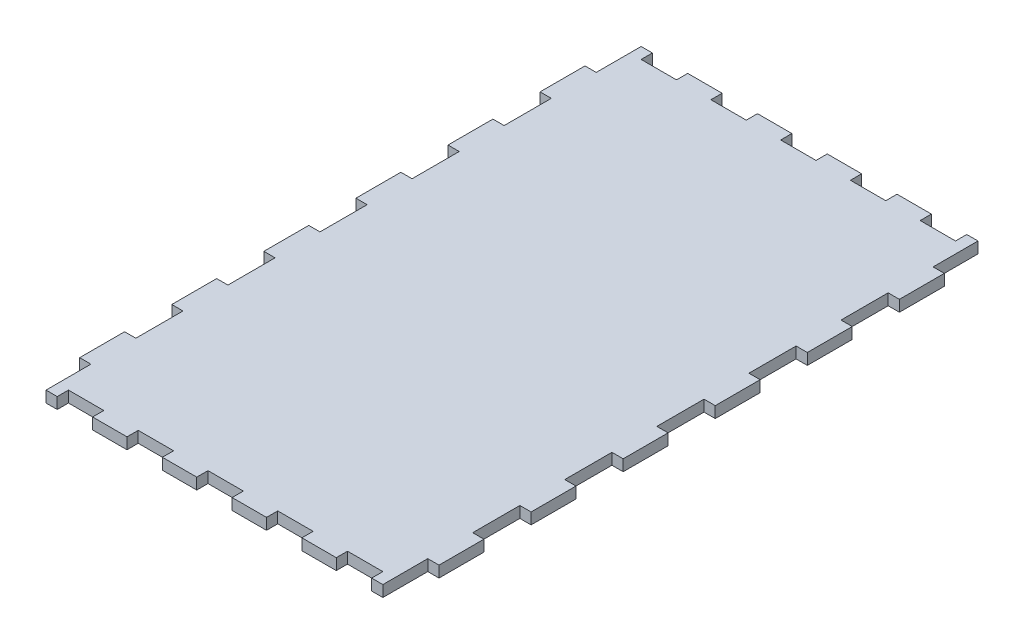
SolidWorks part; units mm, degrees
ref_plane "Front Plane" through (0, 0, 0) normal (0, 0, 1) x (1, 0, 0)
ref_plane "Top Plane" through (0, 0, 0) normal (0, 1, 0) x (1, 0, 0)
ref_plane "Right Plane" through (0, 0, 0) normal (1, 0, 0) x (0, 0, -1)
sketch "Sketch1" plane through (0, 0, 0) normal (0, 1, 0) x (1, 0, 0)
  line L0 (-80, 51.5) -> (-80, 30.5)
  line L1 (-80, 132.5) -> (80, 132.5)
  line L2 (-80, 132.5) -> (-80, -132.5)
  line L3 (-80, -132.5) -> (80, -132.5)
  line L4 (80, 132.5) -> (80, -132.5)
  line L5 (-80, 132.5) -> (80, -132.5) construction
  line L6 (-80, -132.5) -> (80, 132.5) construction
  line L7 (-80, 92.5) -> (-75, 92.5)
  line L8 (-80, 92.5) -> (-80, 71.5)
  line L9 (-80, 71.5) -> (-75, 71.5)
  line L10 (-75, 92.5) -> (-75, 71.5)
  line L11 (-80, 51.5) -> (-75, 51.5)
  line L12 (-75, 51.5) -> (-75, 30.5)
  line L13 (-80, 30.5) -> (-75, 30.5)
  line L14 (-80, 10.5) -> (-80, -10.5)
  line L15 (-80, 10.5) -> (-75, 10.5)
  line L16 (-75, 10.5) -> (-75, -10.5)
  line L17 (-80, -10.5) -> (-75, -10.5)
  line L18 (-80, -30.5) -> (-80, -51.5)
  line L19 (-80, -30.5) -> (-75, -30.5)
  line L20 (-75, -30.5) -> (-75, -51.5)
  line L21 (-80, -51.5) -> (-75, -51.5)
  line L22 (-80, -71.5) -> (-80, -92.5)
  line L23 (-80, -71.5) -> (-75, -71.5)
  line L24 (-75, -71.5) -> (-75, -92.5)
  line L25 (-80, -92.5) -> (-75, -92.5)
  line L26 (0, 132.5) -> (0, -132.5) construction
  line L27 (-80, 132.5) -> (-75, 132.5)
  line L28 (-80, 132.5) -> (-80, 112.5)
  line L29 (-80, 112.5) -> (-75, 112.5)
  line L30 (-75, 132.5) -> (-75, 112.5)
  line L31 (-80, -132.5) -> (-75, -132.5)
  line L32 (-80, -132.5) -> (-80, -112.5)
  line L33 (-80, -112.5) -> (-75, -112.5)
  line L34 (-75, -132.5) -> (-75, -112.5)
  line L35 (80, -112.5) -> (75, -112.5)
  line L36 (75, -132.5) -> (75, -112.5)
  line L37 (80, -132.5) -> (75, -132.5)
  line L38 (80, -132.5) -> (80, -112.5)
  line L39 (80, -71.5) -> (75, -71.5)
  line L40 (75, -71.5) -> (75, -92.5)
  line L41 (80, -92.5) -> (75, -92.5)
  line L42 (80, -71.5) -> (80, -92.5)
  line L43 (80, -30.5) -> (75, -30.5)
  line L44 (75, -30.5) -> (75, -51.5)
  line L45 (80, -51.5) -> (75, -51.5)
  line L46 (80, -30.5) -> (80, -51.5)
  line L47 (80, 10.5) -> (75, 10.5)
  line L48 (75, 10.5) -> (75, -10.5)
  line L49 (80, -10.5) -> (75, -10.5)
  line L50 (80, 10.5) -> (80, -10.5)
  line L51 (80, 51.5) -> (75, 51.5)
  line L52 (75, 51.5) -> (75, 30.5)
  line L53 (80, 30.5) -> (75, 30.5)
  line L54 (80, 51.5) -> (80, 30.5)
  line L55 (80, 71.5) -> (75, 71.5)
  line L56 (75, 92.5) -> (75, 71.5)
  line L57 (80, 92.5) -> (75, 92.5)
  line L58 (80, 92.5) -> (80, 71.5)
  line L59 (80, 112.5) -> (75, 112.5)
  line L60 (75, 132.5) -> (75, 112.5)
  line L61 (80, 132.5) -> (75, 132.5)
  line L62 (80, 132.5) -> (80, 112.5)
  line L63 (-38.9375, 132.5) -> (-38.9375, 127.5)
  line L64 (-70, 132.5) -> (-54.25, 132.5)
  line L65 (-70, 132.5) -> (-70, 127.5)
  line L66 (-70, 127.5) -> (-54.25, 127.5)
  line L67 (-54.25, 132.5) -> (-54.25, 127.5)
  line L68 (-38.9375, 132.5) -> (-23.1875, 132.5)
  line L69 (-23.1875, 132.5) -> (-23.1875, 127.5)
  line L70 (-38.9375, 127.5) -> (-23.1875, 127.5)
  line L71 (-7.875, 132.5) -> (-7.875, 127.5)
  line L72 (-7.875, 132.5) -> (7.875, 132.5)
  line L73 (7.875, 132.5) -> (7.875, 127.5)
  line L74 (-7.875, 127.5) -> (7.875, 127.5)
  line L75 (23.1875, 132.5) -> (23.1875, 127.5)
  line L76 (23.1875, 132.5) -> (38.9375, 132.5)
  line L77 (38.9375, 132.5) -> (38.9375, 127.5)
  line L78 (23.1875, 127.5) -> (38.9375, 127.5)
  line L79 (54.25, 132.5) -> (54.25, 127.5)
  line L80 (54.25, 132.5) -> (70, 132.5)
  line L81 (70, 132.5) -> (70, 127.5)
  line L82 (54.25, 127.5) -> (70, 127.5)
  line L83 (-80, 0) -> (80, 0) construction
  line L84 (-7.875, -132.5) -> (7.875, -132.5)
  line L85 (7.875, -132.5) -> (7.875, -127.5)
  line L86 (-7.875, -127.5) -> (7.875, -127.5)
  line L87 (-7.875, -132.5) -> (-7.875, -127.5)
  line L88 (54.25, -132.5) -> (70, -132.5)
  line L89 (70, -132.5) -> (70, -127.5)
  line L90 (54.25, -127.5) -> (70, -127.5)
  line L91 (54.25, -132.5) -> (54.25, -127.5)
  line L92 (23.1875, -132.5) -> (38.9375, -132.5)
  line L93 (38.9375, -132.5) -> (38.9375, -127.5)
  line L94 (23.1875, -127.5) -> (38.9375, -127.5)
  line L95 (23.1875, -132.5) -> (23.1875, -127.5)
  line L96 (-38.9375, -132.5) -> (-23.1875, -132.5)
  line L97 (-23.1875, -132.5) -> (-23.1875, -127.5)
  line L98 (-38.9375, -127.5) -> (-23.1875, -127.5)
  line L99 (-38.9375, -132.5) -> (-38.9375, -127.5)
  line L100 (-70, -127.5) -> (-54.25, -127.5)
  line L101 (-54.25, -132.5) -> (-54.25, -127.5)
  line L102 (-70, -132.5) -> (-54.25, -132.5)
  line L103 (-70, -132.5) -> (-70, -127.5)
  point P0 (0, 0)
  dimension "D1" = 160
  dimension "D2" = 265
  dimension "D3" = 21
  dimension "D4" = 40
  dimension "D5" = 5
  dimension "D7" = 40
  dimension "D8" = 5
  dimension "D9" = 20
  dimension "D10" = 10
  dimension "D11" = 15.75
  dimension "D12" = 5
  dimension "D14" = 10
  dimension "D6" = 5
  dimension "D13" = 5
extrude "Boss-Extrude1" add sketch "Sketch1" along normal blind 5 contours L3 L103 L100 L101 L99 L98 L97 L87 L86 L85 L95 L94 L93 L91 L90 L89 L36 L35 L4 L41 L40 L39 L45 L44 L43 L49 L48 L47 L53 L52 L51 L55 L56 L57 L59 L60 L1 L81 L82 L79
